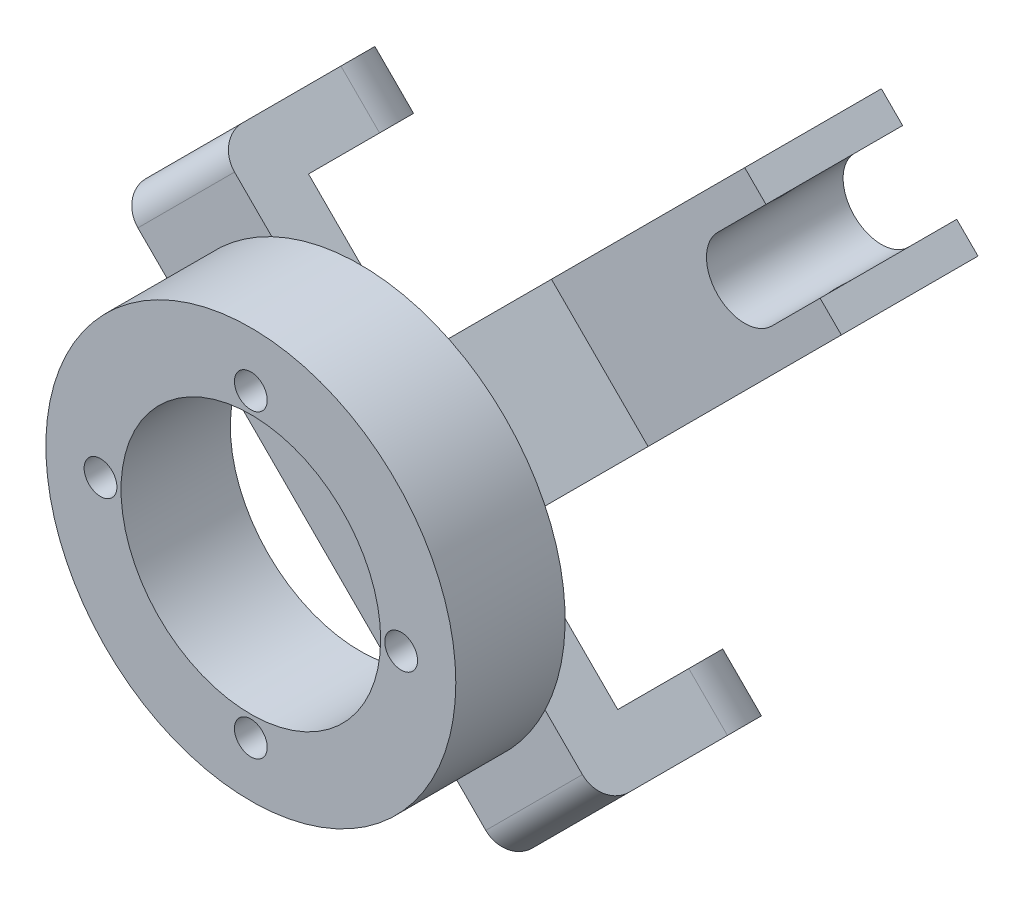
SolidWorks part; units mm, degrees
ref_plane "Płaszczyzna przednia" through (0, 0, 0) normal (0, 0, 1) x (1, 0, 0)
ref_plane "Płaszczyzna górna" through (0, 0, 0) normal (0, 1, 0) x (1, 0, 0)
ref_plane "Płaszczyzna prawa" through (0, 0, 0) normal (1, 0, 0) x (0, 0, -1)
sketch "Szkic1" plane through (0, 0, 0) normal (0, 0, 1) x (1, 0, 0)
  circle A0 centre (0, 0) radius 75
  dimension "D1" = 150
extrude "Dodanie-wyciągnięcie1" add sketch "Szkic1" along normal blind 40
sketch "Szkic2" plane through (0, 0, 40) normal (0, 0, 1) x (1, 0, 0)
  circle A0 centre (-55, 0) radius 6
  circle A1 centre (0, 55) radius 6
  circle A2 centre (55, 0) radius 6
  circle A3 centre (0, -55) radius 6
  point P12 (0, 0)
  dimension "D1" = 12
  dimension "D2" = 55
  dimension "D3" = 4
extrude "Wytnij-wyciągnięcie1" cut sketch "Szkic2" against normal blind 40
sketch "Szkic3" plane through (0, 0, 40) normal (0, 0, 1) x (1, 0, 0)
  circle A0 centre (0, 0) radius 47.5
  dimension "D1" = 95
extrude "Wytnij-wyciągnięcie2" cut sketch "Szkic3" against normal blind 40
ref_plane "Płaszczyzna1" through (0, 0, 0) normal (0.7071, -0.7071, 0) x (-0.7071, -0.7071, 0)
sketch "Szkic4" plane through (0, 0, 0) normal (0.7071, -0.7071, 0) x (-0.7071, -0.7071, 0)
  line L0 (75, 0) -> (-75, 0) construction
  line L1 (-25, 0) -> (25, 0)
  line L2 (-25, 0) -> (-25, 20)
  line L3 (-25, 20) -> (25, 20)
  line L4 (25, 0) -> (25, 20)
  dimension "D1" = 25
  dimension "D2" = 50
  dimension "D3" = 20
extrude "Dodanie-wyciągnięcie2" add sketch "Szkic4" along normal mid plane 200
sketch "Szkic6" plane through (70.7107, -70.7107, 0) normal (0.7071, -0.7071, 0) x (0, 0, -1)
  line L1 (20, 25) -> (70, 25)
  line L2 (20, 25) -> (20, -24.9998)
  line L3 (20, -24.9998) -> (70, -24.9998)
  line L4 (70, 25) -> (70, -24.9998)
  dimension "D1" = 50
extrude "Dodanie-wyciągnięcie3" add sketch "Szkic6" against normal blind 20
mirror "Lustro1" about plane through (0, 0, 0) normal (0.7071, -0.7071, 0) of "Dodanie-wyciągnięcie3"
sketch "Szkic7" plane through (-70.7107, 70.7107, 0) normal (-0.7071, 0.7071, 0) x (0, 0, 1)
  line L0 (-70, -24.9998) -> (-70, 25) construction
  circle A0 centre (-45, 0) radius 7
  dimension "D1" = 14
  dimension "D2" = 25
extrude "Wytnij-wyciągnięcie3" cut sketch "Szkic7" against normal through all
fillet "Zaokrąglenie1" radius 24 4 edges at (45.9621, -81.3171, -70) (81.3173, -45.9619, -70) (-45.9619, 81.3173, -70) (-81.3171, 45.9621, -70)
fillet "Zaokrąglenie2" radius 10 2 edges at (-70.7107, 70.7107, 0) (70.7107, -70.7107, 0)
sketch "Szkic8" plane through (0, 0, -20) normal (0, 0, -1) x (-1, 0, 0)
  line L0 (0, 35.3553) -> (35.3553, 0)
  line L1 (0, 60.5) -> (0, -60.5) construction
  line L2 (60.5, 0) -> (-60.5, 0) construction
  line L3 (35.3553, 0) -> (0, -35.3553)
  line L4 (-53.033, -88.3883) -> (88.3883, 53.033) construction
  line L5 (0, -35.3553) -> (-35.3553, 0)
  line L6 (-35.3553, 0) -> (0, 35.3553)
  dimension "D1" = 50
  dimension "D2" = 50
extrude "Dodanie-wyciągnięcie4" add sketch "Szkic8" along normal blind 100
sketch "Szkic10" plane through (17.6777, 17.6777, 0) normal (0.7071, 0.7071, 0) x (0, 0, -1)
  line L0 (120, -25) -> (20, -25) construction
  line L1 (120, 25) -> (70, 25)
  line L2 (120, 25) -> (120, -25)
  line L3 (120, -25) -> (70, -25)
  line L4 (70, 25) -> (70, -25)
  dimension "D1" = 50
extrude "Dodanie-wyciągnięcie5" add sketch "Szkic10" along normal blind 100
sketch "Szkic12" plane through (17.6777, -17.6777, 0) normal (0.7071, -0.7071, 0) x (0, 0, -1)
  line L1 (70, 125) -> (70, 25) construction
  line L4 (70, 125) -> (120, 125) construction
  circle A0 centre (95, 105) radius 7
  dimension "D3" = 14
  dimension "D1" = 25
  dimension "D2" = 20
extrude "Wytnij-wyciągnięcie5" cut sketch "Szkic12" against normal through all
sketch "Szkic14" plane through (0, 0, -120) normal (0, 0, -1) x (-1, 0, 0)
  line L0 (-38.8909, 38.8909) -> (38.8909, -38.8909) construction
  line L1 (-106.066, 70.7107) -> (-70.7107, 106.066) construction
  line L3 (35.3553, 0) -> (-70.7107, 106.066) construction
  line L7 (-80.6102, 60.8112) -> (-98.2878, 78.4889)
  line L10 (-60.8112, 80.6102) -> (-78.4889, 98.2878)
  line L11 (-78.4889, 98.2878) -> (-98.2878, 78.4889)
  arc A0 (-80.6102, 60.8112) -> (-60.8112, 80.6102) centre (-70.7107, 70.7107) ccw
  dimension "D1" = 28
  dimension "D2" = 25
  dimension "D3" = 25
extrude "Wytnij-wyciągnięcie6" cut sketch "Szkic14" against normal through all
